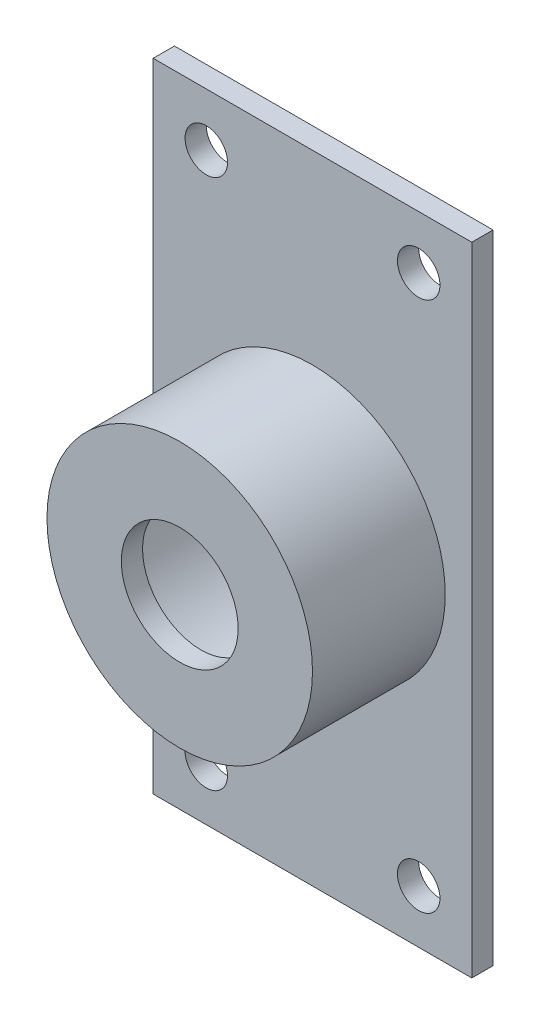
SolidWorks part; units mm, degrees
ref_plane "Front Plane" through (0, 0, 0) normal (0, 0, 1) x (1, 0, 0)
ref_plane "Top Plane" through (0, 0, 0) normal (0, 1, 0) x (1, 0, 0)
ref_plane "Right Plane" through (0, 0, 0) normal (1, 0, 0) x (0, 0, -1)
sketch "Sketch1" plane through (0, 0, 0) normal (0, 0, 1) x (1, 0, 0)
  line L1 (-30, -60) -> (30, -60)
  line L2 (-30, -60) -> (-30, 60)
  line L3 (-30, 60) -> (30, 60)
  line L4 (30, -60) -> (30, 60)
  line L5 (-30, -60) -> (30, 60) construction
  line L6 (-30, 60) -> (30, -60) construction
  point P0 (0, 0)
  dimension "D1" = 60
  dimension "D2" = 120
extrude "Boss-Extrude1" add sketch "Sketch1" along normal blind 4
sketch "Sketch2" plane through (0, 0, 4) normal (0, 0, 1) x (1, 0, 0)
  line L0 (-30, 60) -> (-30, -60) construction
  line L1 (30, 60) -> (-30, 60) construction
  circle A0 centre (-20, 50) radius 4
  circle A1 centre (20, 50) radius 4
  circle A2 centre (20, -50) radius 4
  circle A3 centre (-20, -50) radius 4
  dimension "D1" = 10
  dimension "D2" = 10
  dimension "D3" = 2
  dimension "D4" = 2
extrude "Cut-Extrude1" cut sketch "Sketch2" against normal blind 4
sketch "Sketch3" plane through (0, 0, 4) normal (0, 0, 1) x (1, 0, 0)
  circle A0 centre (0, 0) radius 25
extrude "Boss-Extrude2" add sketch "Sketch3" along normal blind 25
sketch "Sketch4" plane through (0, 0, 0) normal (0, 0, -1) x (-1, 0, 0)
  circle A0 centre (0, 0) radius 21.6
extrude "Cut-Extrude2" cut sketch "Sketch4" against normal blind 25
sketch "Sketch5" plane through (0, 0, 29) normal (0, 0, 1) x (1, 0, 0)
  circle A0 centre (0, 0) radius 11
extrude "Cut-Extrude3" cut sketch "Sketch5" against normal blind 25
